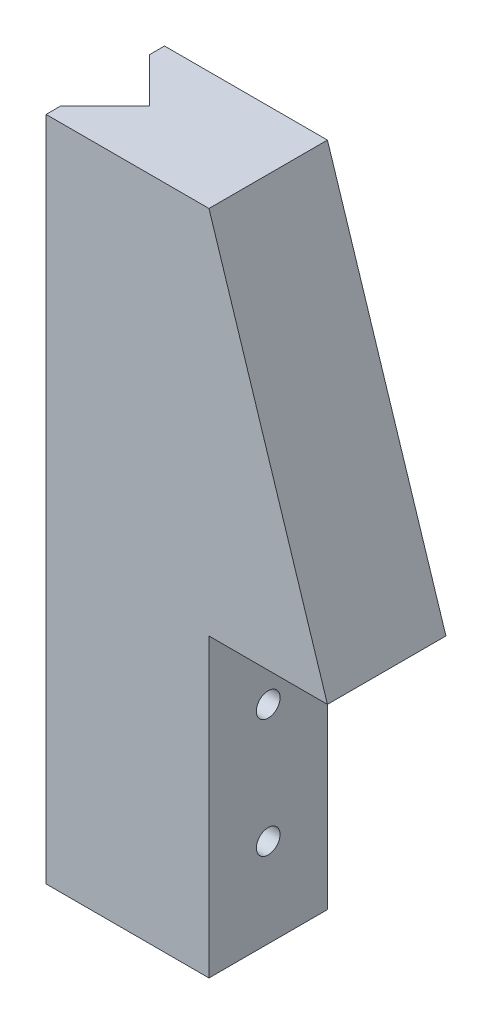
SolidWorks part; units mm, degrees
material "POM Acetal Copolymer"
ref_plane "正面" through (0, 0, 0) normal (0, 0, 1) x (1, 0, 0)
ref_plane "平面" through (0, 0, 0) normal (0, 1, 0) x (1, 0, 0)
ref_plane "右側面" through (0, 0, 0) normal (1, 0, 0) x (0, 0, -1)
sketch "Sketch1" plane through (0, 0, 0) normal (0, 0, 1) x (1, 0, 0)
  line L0 (0, 0) -> (-8, 0)
  line L1 (-8, 0) -> (-8, -20)
  line L2 (-8, -20) -> (-19, -20)
  line L3 (-19, -20) -> (-19, 25)
  line L4 (-19, 25) -> (-8, 25)
  line L5 (-8, 25) -> (0, 0)
  dimension "D1" = 20
  dimension "D2" = 45
extrude "Boss-Extrude1" add sketch "Sketch1" along normal blind 8
sketch "Sketch2" plane through (0, 25, 0) normal (0, 1, 0) x (1, 0, 0)
  line L0 (-19, -4) -> (-19, -1)
  line L1 (-19, -8) -> (-19, 0) construction
  line L2 (-19, -1) -> (-16, -4)
  line L3 (-16, -4) -> (-19, -7)
  line L4 (-19, -7) -> (-19, -4)
extrude "Cut-Extrude1" cut sketch "Sketch2" against normal through all
hole_wizard "M2x0.4 Tapped Hole1" positions "3DSketch1" profile "Sketch3" tap size "M2x0.4" standard "JIS"
sketch3d "3DSketch1"
  line L0 (-8, -20, 8) -> (-8, 0, 8) construction
  line L3 (-8, 0, 8) -> (-8, 0, 0) construction
  point P0 (-8, -6, 4)
  point P2 (-8, -14, 4)
  dimension "D1" = 4
  dimension "D2" = 6
  dimension "D3" = 14
  dimension "D4" = 4
cosmetic thread "Hole Thread1" parameters "D1"=4.6, "D2"=2
cosmetic thread "Hole Thread2" parameters "D1"=4.6, "D2"=2
sketch "Sketch3" plane through (-8, -6, 4) normal (0, 1, 0) x (0, 0, -1)
  line L0 (0, 0) -> (0, 5.4807)
  line L1 (0, 5.4807) -> (0.8, 5)
  line L2 (0.8, 5) -> (0.8, 0)
  line L5 (0.8, 0) -> (0, 0)
  line L10 (0, 5.4807) -> (-0.8, 5) construction
  line L11 (0, -6.35) -> (0, 107.95) construction
  dimension "Tap Drill Dia." = 1.6
  dimension "Tap Drill Depth" = 5
  dimension "Drill Angle" = 118
